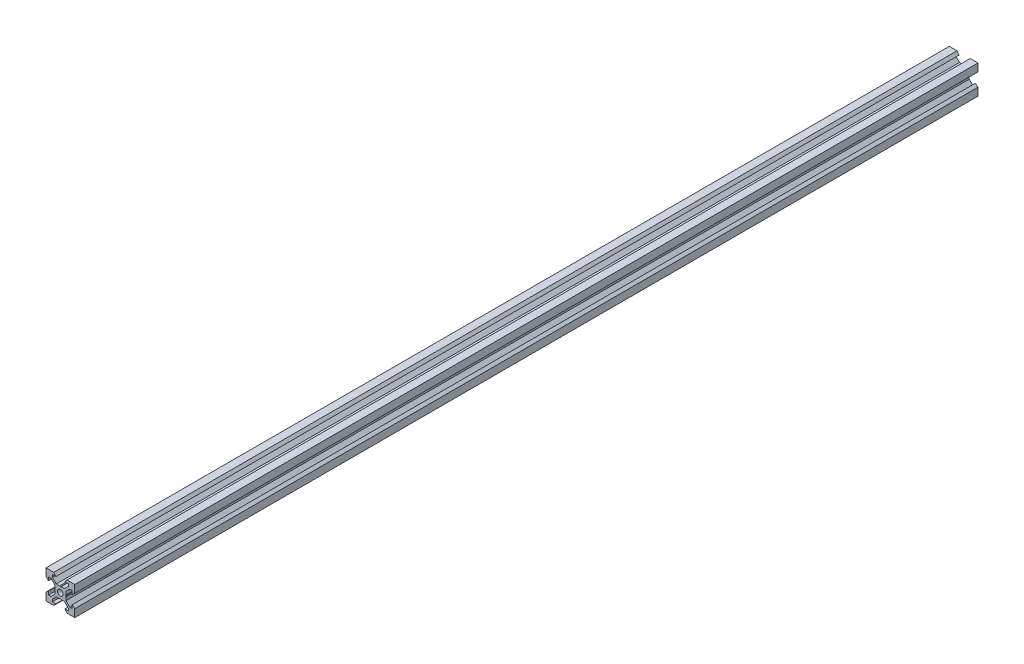
SolidWorks part; units mm, degrees
ref_plane "Front Plane" through (0, 0, 0) normal (0, 0, 1) x (1, 0, 0)
ref_plane "Top Plane" through (0, 0, 0) normal (0, 1, 0) x (1, 0, 0)
ref_plane "Right Plane" through (0, 0, 0) normal (1, 0, 0) x (0, 0, -1)
sketch "Sketch1" plane through (0, 0, 0) normal (0, 0, 1) x (1, 0, 0)
  line L0 (10, 10) -> (4.6104, 10) construction
  line L1 (10, 10) -> (10, 4.6104) construction
  line L2 (10, -10) -> (10, -4.6104) construction
  line L3 (10, -10) -> (4.6104, -10) construction
  line L4 (10, 10) -> (10, 4.6104)
  line L5 (6.5607, 5.5) -> (8.2, 5.5)
  line L6 (5.5, 8.2) -> (5.5, 6.5607)
  line L7 (10, 10) -> (4.6104, 10)
  line L8 (10, 10) -> (10, 4.6104)
  line L9 (6.5607, 5.5) -> (3.9, 2.8393)
  line L10 (5.5, 6.5607) -> (2.8393, 3.9)
  line L11 (10, 4.6104) -> (8.2, 3.1)
  line L12 (4.6104, 10) -> (3.1, 8.2)
  line L13 (8.2, 3.1) -> (8.2, 5.5)
  line L14 (3.1, 8.2) -> (5.5, 8.2)
  line L15 (-6.5607, 5.5) -> (-8.2, 5.5)
  line L16 (6.5607, -5.5) -> (8.2, -5.5)
  line L17 (3.1, -8.2) -> (5.5, -8.2)
  line L18 (8.2, -3.1) -> (8.2, -5.5)
  line L19 (4.6104, -10) -> (3.1, -8.2)
  line L20 (10, -4.6104) -> (8.2, -3.1)
  line L21 (0.5196, -3.9) -> (0, -3.6)
  line L22 (0.5196, 3.9) -> (0, 3.6)
  line L23 (3.6, 0) -> (3.9, -0.5196)
  line L24 (3.9, 0.5196) -> (3.6, 0)
  line L25 (3.9, 0.5196) -> (3.9, 2.8393)
  line L26 (2.8393, 3.9) -> (0.5196, 3.9)
  line L27 (3.9, -2.8393) -> (3.9, -0.5196)
  line L28 (2.8393, -3.9) -> (0.5196, -3.9)
  line L29 (5.5, -6.5607) -> (2.8393, -3.9)
  line L30 (6.5607, -5.5) -> (3.9, -2.8393)
  line L31 (10, -10) -> (10, -4.6104)
  line L32 (10, -10) -> (4.6104, -10)
  line L33 (5.5, -8.2) -> (5.5, -6.5607)
  line L34 (-6.5607, -5.5) -> (-8.2, -5.5)
  line L35 (10, -10) -> (10, -4.6104)
  line L36 (0, 0) -> (0, 8.2) construction
  line L37 (-10, -10) -> (-4.6104, -10) construction
  line L38 (-10, -10) -> (-10, -4.6104) construction
  line L39 (-10, 10) -> (-10, 4.6104) construction
  line L40 (-10, 10) -> (-4.6104, 10) construction
  line L41 (-10, -10) -> (-10, -4.6104)
  line L43 (-5.5, -8.2) -> (-5.5, -6.5607)
  line L44 (-10, -10) -> (-4.6104, -10)
  line L45 (-10, -10) -> (-10, -4.6104)
  line L46 (-6.5607, -5.5) -> (-3.9, -2.8393)
  line L47 (-5.5, -6.5607) -> (-2.8393, -3.9)
  line L48 (-2.8393, -3.9) -> (-0.5196, -3.9)
  line L49 (-3.9, -2.8393) -> (-3.9, -0.5196)
  line L50 (-2.8393, 3.9) -> (-0.5196, 3.9)
  line L51 (-3.9, 0.5196) -> (-3.9, 2.8393)
  line L52 (-3.9, 0.5196) -> (-3.6, 0)
  line L53 (-3.6, 0) -> (-3.9, -0.5196)
  line L54 (-0.5196, 3.9) -> (0, 3.6)
  line L55 (-0.5196, -3.9) -> (0, -3.6)
  line L56 (-10, -4.6104) -> (-8.2, -3.1)
  line L57 (-4.6104, -10) -> (-3.1, -8.2)
  line L58 (-8.2, -3.1) -> (-8.2, -5.5)
  line L59 (-3.1, -8.2) -> (-5.5, -8.2)
  line L60 (-10, -10) -> (10, -10) construction
  line L61 (-10, -10) -> (-10, 10) construction
  line L62 (-3.1, 8.2) -> (-5.5, 8.2)
  line L63 (-8.2, 3.1) -> (-8.2, 5.5)
  line L64 (-4.6104, 10) -> (-3.1, 8.2)
  line L65 (-10, 4.6104) -> (-8.2, 3.1)
  line L66 (-5.5, 6.5607) -> (-2.8393, 3.9)
  line L67 (-6.5607, 5.5) -> (-3.9, 2.8393)
  line L68 (-10, 10) -> (-10, 4.6104)
  line L69 (-10, 10) -> (-4.6104, 10)
  line L70 (-5.5, 8.2) -> (-5.5, 6.5607)
  line L71 (-10, 10) -> (10, 10) construction
  line L72 (-10, 10) -> (-10, 4.6104)
  line L73 (10, -10) -> (10, 10) construction
  line L74 (-10, -10) -> (10, 10) construction
  line L75 (-10, 10) -> (10, -10) construction
  circle A0 centre (0, 0) radius 2
  dimension "D7" = 4
  dimension "D1" = 20
  dimension "D2" = 5.3896
  dimension "D3" = 4.5
  dimension "D4" = 50
  dimension "D5" = 1.8
  dimension "D6" = 1.5104
  dimension "D8" = 5.5
  dimension "D9" = 120
  dimension "D10" = 0.3
  dimension "D11" = 2.3197
  dimension "D12" = 7.8
  dimension "D13" = 7.8
  dimension "D14" = 1.5
  dimension "D15" = 2.6607
extrude "Boss-Extrude1" add sketch "Sketch1" along normal mid plane 628.38 contours L70 L62 L64 L69 L68 L65 L63 L15 L67 L51 L52 L53 L49 L46 L34 L58 L56 L41 L44 L57 L59 L43 L47 L48 L55 L21 L28 L29 L33 L17 L19 L32 L31 L20 L18 L16 L30 L27 L23 L24 L25 L9 L5 L13 L11 L4 L7 L12 L14 L6 L10
